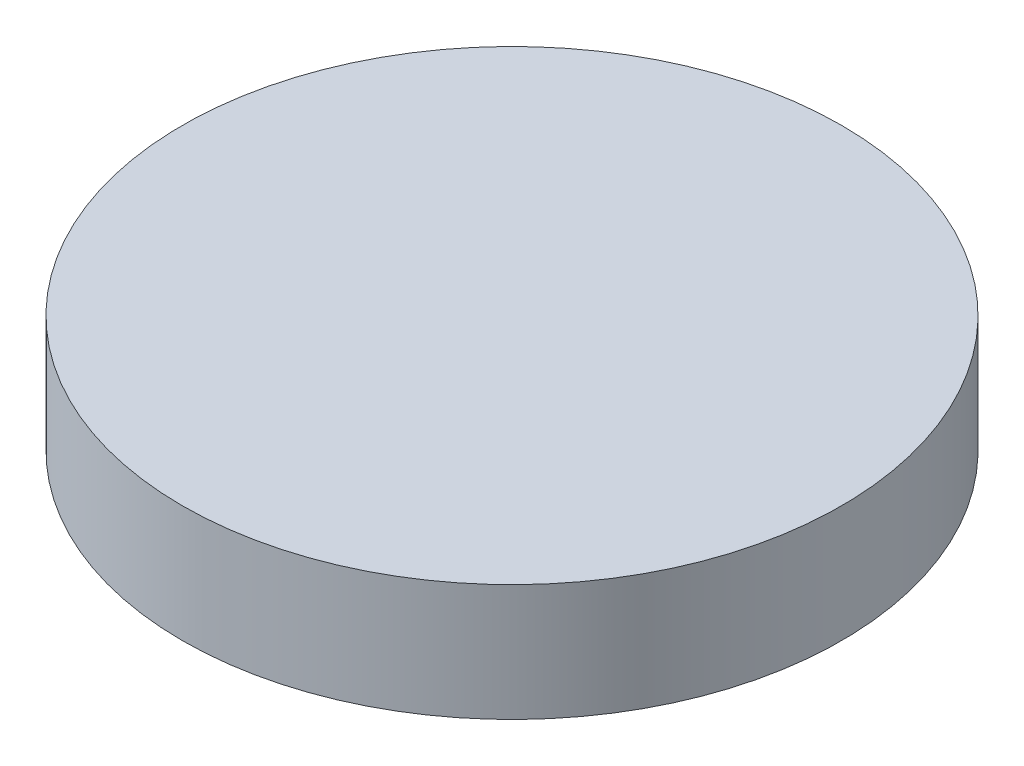
SolidWorks part; units mm, degrees
ref_plane "Front Plane" through (0, 0, 0) normal (0, 0, 1) x (1, 0, 0)
ref_plane "Top Plane" through (0, 0, 0) normal (0, 1, 0) x (1, 0, 0)
ref_plane "Right Plane" through (0, 0, 0) normal (1, 0, 0) x (0, 0, -1)
sketch "Sketch1" plane through (0, 0, 0) normal (0, 1, 0) x (1, 0, 0)
  circle A0 centre (0, 5.9514) radius 40.35
  dimension "D1" = 80.7
extrude "Boss-Extrude1" add sketch "Sketch1" along normal blind 14.3
